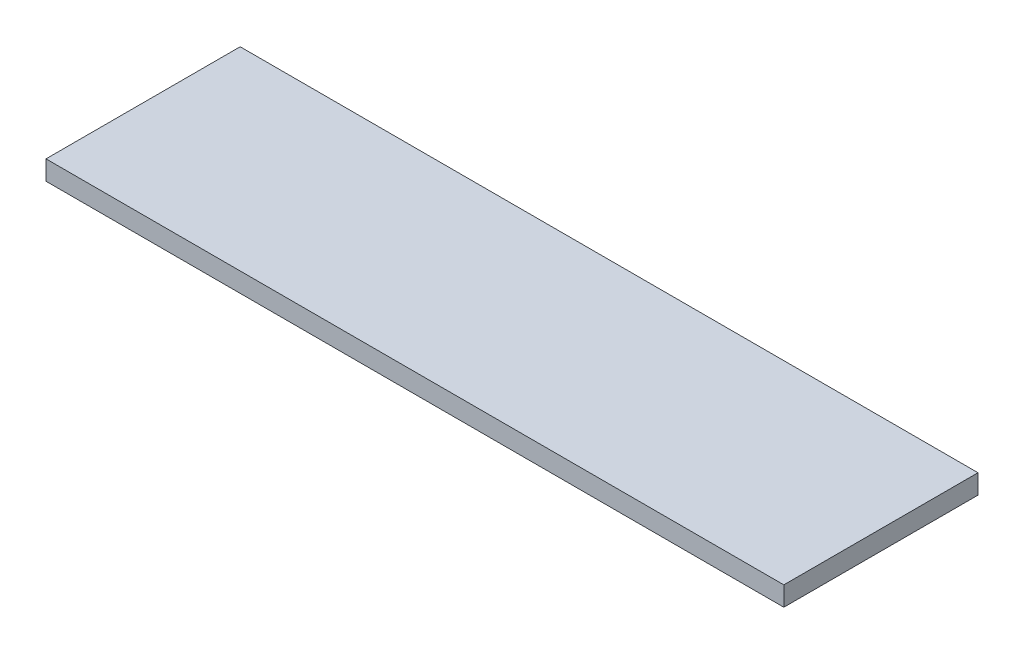
SolidWorks part; units mm, degrees
ref_plane "Front Plane" through (0, 0, 0) normal (0, 0, 1) x (1, 0, 0)
ref_plane "Top Plane" through (0, 0, 0) normal (0, 1, 0) x (1, 0, 0)
ref_plane "Right Plane" through (0, 0, 0) normal (1, 0, 0) x (0, 0, -1)
sketch "Sketch1" plane through (0, 0, 0) normal (0, 1, 0) x (1, 0, 0)
  line L1 (0, 0) -> (3800, 0)
  line L2 (0, 0) -> (0, 1000)
  line L3 (0, 1000) -> (3800, 1000)
  line L4 (3800, 0) -> (3800, 1000)
extrude "Boss-Extrude1" add sketch "Sketch1" along normal blind 100
